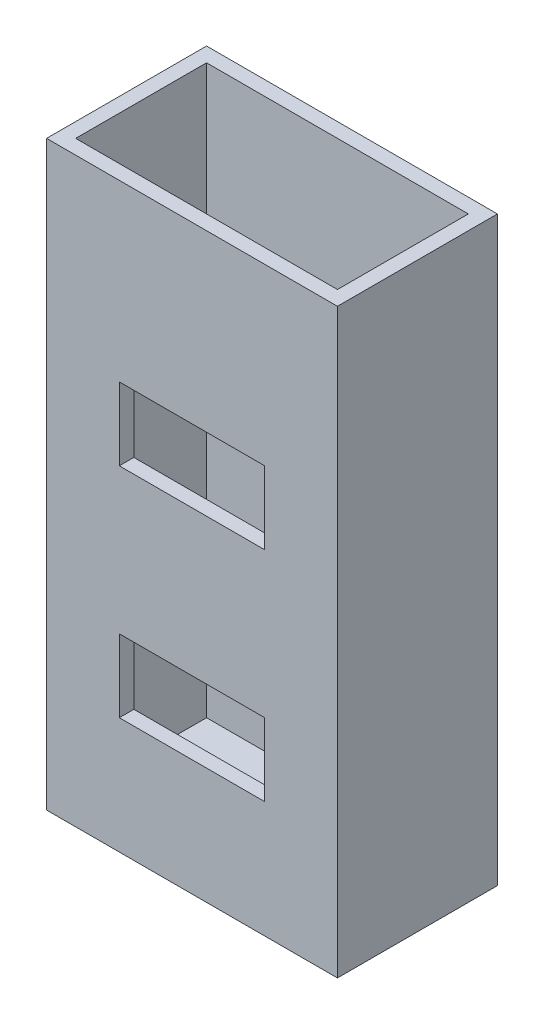
SolidWorks part; units mm, degrees
ref_plane "Front Plane" through (0, 0, 0) normal (0, 0, 1) x (1, 0, 0)
ref_plane "Top Plane" through (0, 0, 0) normal (0, 1, 0) x (1, 0, 0)
ref_plane "Right Plane" through (0, 0, 0) normal (1, 0, 0) x (0, 0, -1)
sketch "Sketch1" plane through (0, 0, 0) normal (0, 0, 1) x (1, 0, 0)
  line L1 (-25.9097, 30.4024) -> (-5.9097, 30.4024)
  line L2 (-25.9097, 30.4024) -> (-25.9097, -9.5976)
  line L3 (-25.9097, -9.5976) -> (-5.9097, -9.5976)
  line L4 (-5.9097, 30.4024) -> (-5.9097, -9.5976)
  line L5 (-25.9097, 30.4024) -> (-5.9097, -9.5976) construction
  line L6 (-25.9097, -9.5976) -> (-5.9097, 30.4024) construction
  point P0 (-15.9097, 10.4024)
extrude "Boss-Extrude1" add sketch "Sketch1" along normal blind 11
sketch "Sketch2" plane through (0, 30.4024, 0) normal (0, 1, 0) x (1, 0, 0)
  line L0 (-25.9097, -11) -> (-25.9097, 0) construction
  line L1 (-24.9097, -1) -> (-6.9097, -1)
  line L2 (-24.9097, -1) -> (-24.9097, -10)
  line L3 (-24.9097, -10) -> (-6.9097, -10)
  line L4 (-6.9097, -1) -> (-6.9097, -10)
  line L5 (-24.9097, -1) -> (-6.9097, -10) construction
  line L6 (-24.9097, -10) -> (-6.9097, -1) construction
  line L7 (-5.9097, -11) -> (-25.9097, -11) construction
  line L8 (-5.9097, 0) -> (-25.9097, 0) construction
  line L9 (-5.9097, -11) -> (-5.9097, 0) construction
  point P0 (-15.9097, -5.5)
  dimension "D1" = 1
  dimension "D2" = 1
  dimension "D3" = 1
  dimension "D4" = 1
extrude "Cut-Extrude1" cut sketch "Sketch2" against normal offset from surface (39 mm away) 1 up to face at (-15.9097, -9.5976, 5.5)
sketch "Sketch3" plane through (0, 0, 11) normal (0, 0, 1) x (1, 0, 0)
  line L0 (-25.9097, 30.4024) -> (-25.9097, -9.5976) construction
  line L1 (-20.9097, 18.4024) -> (-10.9097, 18.4024)
  line L2 (-20.9097, 18.4024) -> (-20.9097, 13.4024)
  line L3 (-20.9097, 13.4024) -> (-10.9097, 13.4024)
  line L4 (-10.9097, 18.4024) -> (-10.9097, 13.4024)
  line L5 (-20.9097, 18.4024) -> (-10.9097, 13.4024) construction
  line L6 (-20.9097, 13.4024) -> (-10.9097, 18.4024) construction
  line L7 (-5.9097, -9.5976) -> (-5.9097, 30.4024) construction
  line L8 (-25.9097, -9.5976) -> (-5.9097, -9.5976) construction
  line L13 (-20.9097, 3.4024) -> (-10.9097, 3.4024)
  line L14 (-20.9097, 3.4024) -> (-20.9097, -1.5976)
  line L19 (-20.9097, -1.5976) -> (-10.9097, -1.5976)
  line L20 (-10.9097, 3.4024) -> (-10.9097, -1.5976)
  line L21 (-20.9097, 3.4024) -> (-10.9097, -1.5976) construction
  line L22 (-20.9097, -1.5976) -> (-10.9097, 3.4024) construction
  point P0 (-15.9097, 15.9024)
  point P9 (-15.9097, 0.9024)
  point P15 (0, 0)
  dimension "D1" = 5
  dimension "D2" = 5
  dimension "D3" = 5
  dimension "D4" = 5
  dimension "D5" = 10
  dimension "D6" = 8
extrude "Cut-Extrude2" cut sketch "Sketch3" against normal blind 4 and the other way blind 6
